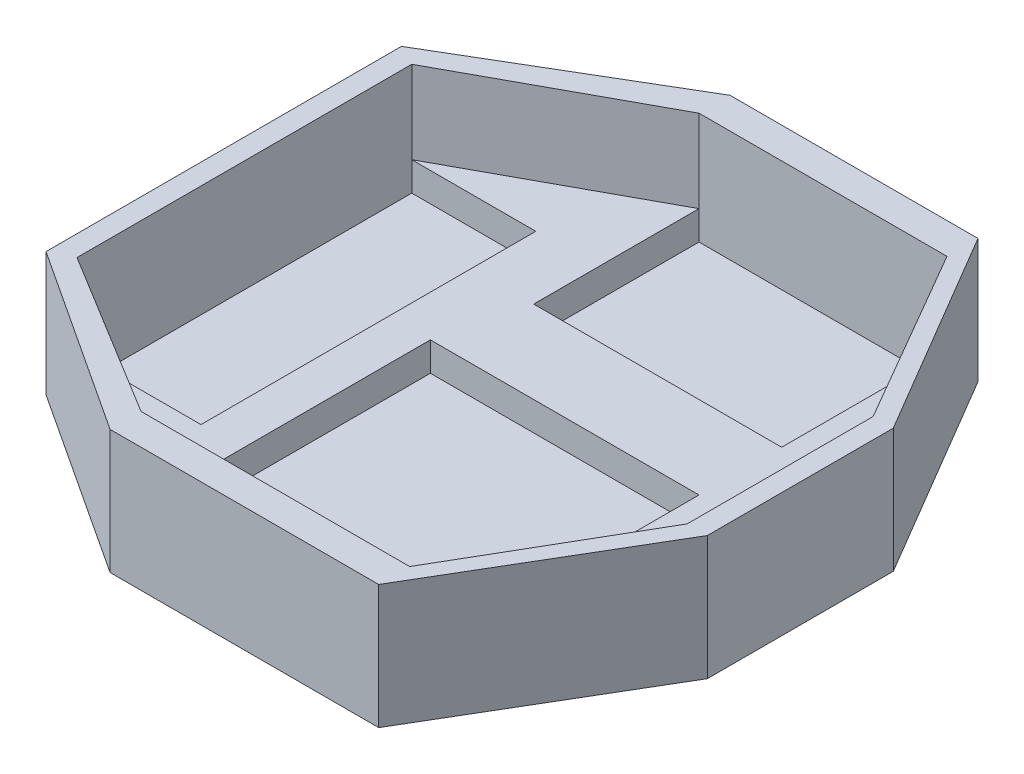
SolidWorks part; units mm, degrees
ref_plane "Front Plane" through (0, 0, 0) normal (0, 0, 1) x (1, 0, 0)
ref_plane "Top Plane" through (0, 0, 0) normal (0, 1, 0) x (1, 0, 0)
ref_plane "Right Plane" through (0, 0, 0) normal (1, 0, 0) x (0, 0, -1)
sketch "Sketch1" plane through (0, 0, 0) normal (0, 1, 0) x (1, 0, 0)
  circle A0 centre (0, 0) radius 85
  dimension "D1" = 170
extrude "Boss-Extrude2" add sketch "Sketch1" along normal blind 10
sketch "Sketch3" plane through (0, 10, 0) normal (0, 1, 0) x (1, 0, 0)
  line L1 (-65, 40.5) -> (-35, 40.5)
  line L2 (-65, 40.5) -> (-65, -40.5)
  line L3 (-65, -40.5) -> (-35, -40.5)
  line L4 (-35, 40.5) -> (-35, -40.5)
  line L5 (-20, 65) -> (40, 65)
  line L6 (-20, 65) -> (-20, 25)
  line L7 (-20, 25) -> (40, 25)
  line L8 (40, 65) -> (40, 25)
  line L9 (-25, 5) -> (40, 5)
  line L10 (-25, 5) -> (-25, -65)
  line L11 (-25, -65) -> (40, -65)
  line L12 (40, 5) -> (40, -65)
  dimension "D1" = 30
  dimension "D2" = 81
  dimension "D3" = 40.5
  dimension "D4" = 35
  dimension "D5" = 60
  dimension "D6" = 40
  dimension "D7" = 15
  dimension "D8" = 65
  dimension "D9" = 70
  dimension "D10" = 10
  dimension "D11" = 65
  dimension "D12" = 20
extrude "Cut-Extrude2" cut sketch "Sketch3" against normal blind 7
sketch "Sketch5" plane through (0, 10, 0) normal (0, 1, 0) x (1, 0, 0)
  line L0 (-70, 43) -> (-20, 72.5)
  line L1 (-20, 72.5) -> (40, 72.5)
  line L2 (40, 72.5) -> (69.5, 22.5)
  line L3 (69.5, 22.5) -> (69.5, -22.5)
  line L4 (-25, -72.5) -> (40, -72.5)
  line L5 (40, -72.5) -> (69.5, -22.5)
  line L6 (-25, -72.5) -> (-70, -43)
  line L7 (-70, -43) -> (-70, 43)
  line L9 (-98.5424, -92.331) -> (95.5207, -92.331)
  line L10 (-98.5424, -92.331) -> (-98.5424, 92.1632)
  line L11 (-98.5424, 92.1632) -> (95.5207, 92.1632)
  line L12 (95.5207, -92.331) -> (95.5207, 92.1632)
  dimension "D1" = 5
  dimension "D2" = 2.5
  dimension "D3" = 2.5
  dimension "D4" = 7.5
  dimension "D5" = 0
  dimension "D6" = 7.5
  dimension "D7" = 0
  dimension "D8" = 65
  dimension "D9" = 0
  dimension "D10" = 29.5
  dimension "D11" = 50
  dimension "D12" = 50
extrude "Cut-Extrude4" cut sketch "Sketch5" against normal blind 10
sketch "Sketch6" plane through (0, 10, 0) normal (0, 1, 0) x (1, 0, 0)
  line L0 (-65, 40.5) -> (-65, -40.5)
  line L1 (-65, -40.5) -> (-25, -65)
  line L2 (-25, -65) -> (40, -65)
  line L3 (40, -65) -> (64.6186, -22.5)
  line L4 (64.6186, -22.5) -> (64.6186, 22.5)
  line L5 (64.6186, 22.5) -> (40, 65)
  line L6 (40, 65) -> (-20, 65)
  line L7 (-20, 65) -> (-65, 40.5)
  line L9 (-70, 43) -> (-20, 72.5)
  line L10 (-20, 72.5) -> (38.2575, 72.5)
  line L11 (40, 72.5) -> (-20, 72.5) construction
  line L12 (38.2575, 72.5) -> (40, 72.5)
  line L13 (40, 72.5) -> (69.5, 22.5)
  line L14 (69.5, 22.5) -> (69.5, -22.5)
  line L15 (69.5, -22.5) -> (40, -72.5)
  line L16 (40, -72.5) -> (-25, -72.5)
  line L17 (-25, -72.5) -> (-70, -43)
  line L18 (-70, -43) -> (-70, 43)
  dimension "D1" = 0
  dimension "D2" = 0
extrude "Boss-Extrude3" add sketch "Sketch6" along normal blind 20
